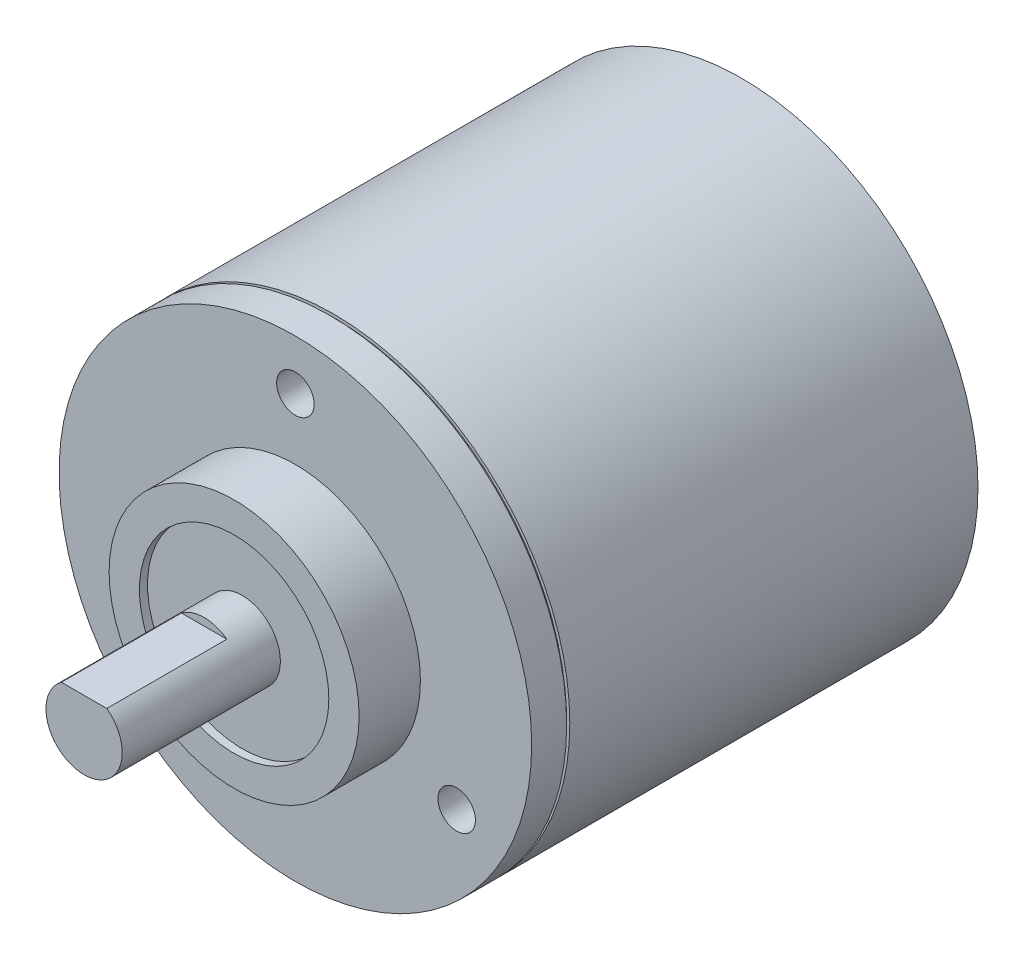
SolidWorks part; units mm, degrees
ref_plane "Plan de face" through (0, 0, 0) normal (0, 0, 1) x (1, 0, 0)
ref_plane "Plan de dessus" through (0, 0, 0) normal (0, 1, 0) x (1, 0, 0)
ref_plane "Plan de droite" through (0, 0, 0) normal (1, 0, 0) x (0, 0, -1)
sketch "Esquisse1" plane through (0, 0, 0) normal (0, 0, 1) x (1, 0, 0)
  circle A0 centre (0, 0) radius 18.9
  dimension "D1" = 37.8
extrude "Boss.-Extru.1" add sketch "Esquisse1" along normal blind 35.6 and the other way blind 0.1 contours A0
sketch "Esquisse3" plane through (0, 0, 35.6) normal (0, 0, 1) x (1, 0, 0)
  circle A0 centre (0, 0) radius 10
  dimension "D1" = 20
extrude "Boss.-Extru.3" add sketch "Esquisse3" along normal blind 4.9
sketch "Esquisse4" plane through (0, 0, 40.5) normal (0, 0, 1) x (1, 0, 0)
  circle A0 centre (0, 0) radius 3.05
  dimension "D1" = 6.1
extrude "Boss.-Extru.4" add sketch "Esquisse4" along normal blind 12
sketch "Esquisse5" plane through (0, 0, 35.6) normal (0, 0, 1) x (1, 0, 0)
  circle A0 centre (0, 14.9) radius 1.5
  circle A1 centre (0, 0) radius 10 construction
  dimension "D1" = 3
  dimension "D2" = 14.9
extrude "Enlèv. mat.-Extru.1" cut sketch "Esquisse5" against normal blind 8
sketch "Esquisse6" plane through (0, 0, 40.5) normal (0, 0, 1) x (1, 0, 0)
  circle A0 centre (0, 0) radius 7.575
  circle A1 centre (0, 0) radius 3.05
  dimension "D1" = 15.15
extrude "Enlèv. mat.-Extru.3" cut sketch "Esquisse6" against normal blind 0.65
sketch "Esquisse7" plane through (0, 0, 52.5) normal (0, 0, 1) x (1, 0, 0)
  line L0 (-4.3171, 2.45) -> (4.5179, 2.45)
  line L1 (4.5179, 2.45) -> (1.4809, 5.487)
  line L2 (1.4809, 5.487) -> (-3.3633, 5.487)
  line L3 (-3.3633, 5.487) -> (-4.3171, 2.45)
  dimension "D1" = 2.45
extrude "Enlèv. mat.-Extru.4" cut sketch "Esquisse7" against normal blind 9.6
pattern_circular "Répétition circulaire1" count 3 every 120 about axis through (0, 0, 0) along (0, 0, 1) of "Enlèv. mat.-Extru.1"
sketch "Esquisse8" plane through (0, 0, 0) normal (1, 0, 0) x (0, 0, -1)
  line L0 (-35.6, 18.9) -> (-35.6, -18.9) construction
  line L1 (-32.8, 21.8462) -> (-32.55, 21.8462)
  line L2 (-32.8, 21.8462) -> (-32.8, 18.65)
  line L3 (-32.8, 18.65) -> (-32.55, 18.65)
  line L4 (-32.55, 21.8462) -> (-32.55, 18.65)
  line L5 (0.1, 18.9) -> (-35.6, 18.9) construction
  dimension "D1" = 2.8
  dimension "D2" = 0.25
  dimension "D3" = 0.25
revolve "Enlèvement de matière-Révolution1" cut sketch "Esquisse8" angle 360 about axis through (0, 0, -0.1) along (0, 0, 1)
